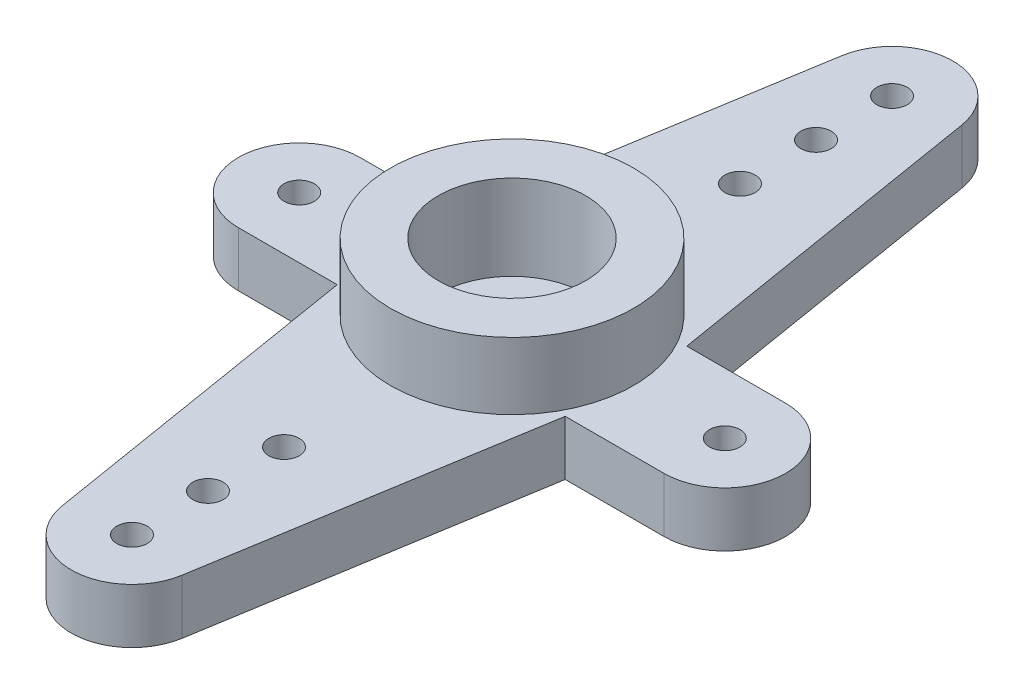
SolidWorks part; units mm, degrees
ref_plane "Front Plane" through (0, 0, 0) normal (0, 0, 1) x (1, 0, 0)
ref_plane "Top Plane" through (0, 0, 0) normal (0, 1, 0) x (1, 0, 0)
ref_plane "Right Plane" through (0, 0, 0) normal (1, 0, 0) x (0, 0, -1)
sketch "Sketch1" plane through (0, 0, 0) normal (0, 1, 0) x (1, 0, 0)
  line L0 (-7, 0) -> (7, 0) construction
  line L1 (-9, -2) -> (9, -2) construction
  line L2 (-9, -2) -> (-9, 2) construction
  line L3 (-9, 2) -> (9, 2) construction
  line L4 (9, -2) -> (9, 2) construction
  line L5 (-9, -2) -> (9, 2) construction
  line L6 (-9, 2) -> (9, -2) construction
  line L7 (-7, 2) -> (7, 2) construction
  line L8 (-7, -2) -> (7, -2) construction
  line L9 (0, 0) -> (0, 4.5567) construction
  line L10 (-3.75, 2) -> (-1.9736, 12.8239)
  line L11 (3.75, 2) -> (1.9736, 12.8239)
  line L12 (-3.75, -2) -> (-1.9736, -12.8239)
  line L13 (3.75, -2) -> (1.9736, -12.8239)
  line L14 (-3.75, 2) -> (-7, 2)
  line L15 (-3.75, -2) -> (-7, -2)
  line L16 (3.75, 2) -> (7, 2)
  line L17 (3.75, -2) -> (7, -2)
  arc A0 (-7, 2) -> (-7, -2) centre (-7, 0) ccw construction
  arc A1 (7, -2) -> (7, 2) centre (7, 0) ccw construction
  circle A2 centre (0, -12.5) radius 2 construction
  circle A3 centre (0, 12.5) radius 2 construction
  arc A4 (-1.9736, -12.8239) -> (1.9736, -12.8239) centre (0, -12.5) ccw
  arc A5 (-1.9736, 12.8239) -> (1.9736, 12.8239) centre (0, 12.5) cw
  arc A6 (-7, 2) -> (-7, -2) centre (-7, 0) ccw
  arc A7 (7, 2) -> (7, -2) centre (7, 0) cw
  point P0 (0, 0)
  point P8 (0, 0)
  dimension "D4" = 29
  dimension "D5" = 4
  dimension "D1" = 4
  dimension "D2" = 18
  dimension "D3" = 7.5
extrude "Boss-Extrude1" add sketch "Sketch1" along normal blind 1.8
sketch "Sketch2" plane through (0, 1.8, 0) normal (0, 1, 0) x (1, 0, 0)
  circle A0 centre (0, 0) radius 4
  dimension "D1" = 8
extrude "Boss-Extrude2" add sketch "Sketch2" along normal offset from surface (2.2 mm away) 4 up to face at (0, 0, 0)
sketch "Sketch3" plane through (0, 4, 0) normal (0, 1, 0) x (1, 0, 0)
  circle A0 centre (0, 0) radius 2.425
  dimension "D1" = 4.85
extrude "Cut-Extrude1" cut sketch "Sketch3" against normal blind 2.8
sketch "Sketch4" plane through (0, 1.8, 0) normal (0, 1, 0) x (1, 0, 0)
  line L0 (0, 0) -> (0, 5.3168) construction
  line L1 (0, 0) -> (2.1944, 0) construction
  circle A0 centre (-7, 0) radius 0.5
  circle A1 centre (7, 0) radius 0.5
  circle A2 centre (0, 7.5) radius 0.5
  circle A3 centre (0, -7.5) radius 0.5
  circle A4 centre (0, 10) radius 0.5
  circle A5 centre (0, 12.5) radius 0.5
  circle A6 centre (0, -10) radius 0.5
  circle A7 centre (0, -12.5) radius 0.5
  dimension "D1" = 14
  dimension "D2" = 1
  dimension "D4" = 1
  dimension "D3" = 15
  dimension "D5" = 5
  dimension "D6" = 2.5
extrude "Cut-Extrude2" cut sketch "Sketch4" against normal through all
